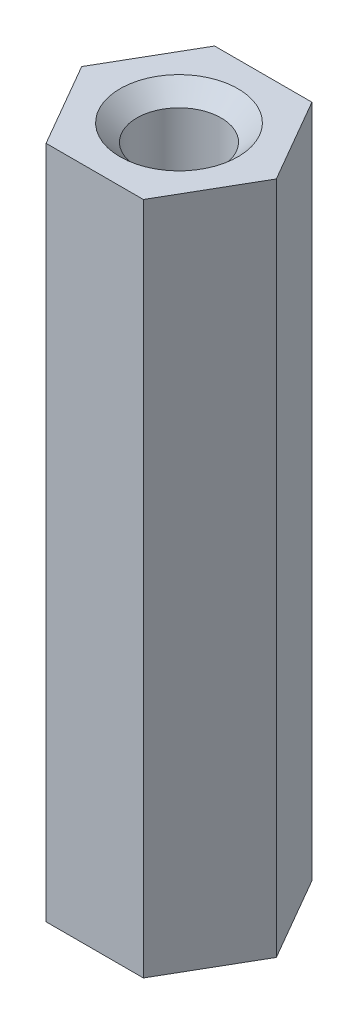
SolidWorks part; units mm, degrees
material "1,0503 (C45)"
ref_plane "Спереди" through (0, 0, 0) normal (0, 0, 1) x (1, 0, 0)
ref_plane "Сверху" through (0, 0, 0) normal (0, 1, 0) x (1, 0, 0)
ref_plane "Справа" through (0, 0, 0) normal (1, 0, 0) x (0, 0, -1)
sketch "Эскиз1" plane through (0, 0, 0) normal (0, 1, 0) x (1, 0, 0)
  line L1 (2.8868, 0) -> (1.4434, 2.5)
  line L2 (1.4434, 2.5) -> (-1.4434, 2.5)
  line L3 (-1.4434, 2.5) -> (-2.8868, 0)
  line L4 (-2.8868, 0) -> (-1.4434, -2.5)
  line L5 (-1.4434, -2.5) -> (1.4434, -2.5)
  line L6 (1.4434, -2.5) -> (2.8868, 0)
  circle A0 centre (0, 0) radius 2.5 construction
  dimension "D1" = 5
extrude "Бобышка-Вытянуть1" add sketch "Эскиз1" along normal blind 20
hole_wizard "Отверстие обработанное метчиком M3x0.51" positions "Эскиз3" profile "Эскиз2" tap size "M3x0.5" standard "Ansi (метрические)" end condition through all
sketch "Эскиз3" plane through (0, 20, 0) normal (0, 1, 0) x (-1, 0, 0)
  point P0 (0, 0)
sketch "Эскиз2" plane through (0, 20, 0) normal (1, 0, 0) x (0, 0, 1)
  line L0 (0, 0) -> (0, 20)
  line L1 (0, 20) -> (1.75, 20)
  line L2 (1.25, 19.5) -> (1.25, 0.5)
  line L3 (1.25, 0.5) -> (1.75, 0)
  line L5 (1.75, 0) -> (0, 0)
  line L6 (-1.25, 0.5) -> (-1.75, 0) construction
  line L7 (1.75, 20) -> (1.25, 19.5)
  line L8 (-1.75, 20) -> (-1.25, 19.5) construction
  line L11 (0, -6.35) -> (0, 107.95) construction
  dimension "Диаметр проходного сверла" = 2.5
  dimension "Глубина проходного сверла" = 20
  dimension "Диаметр передней зенковки" = 3.5
  dimension "Угол передней зенковки" = 90
  dimension "Диаметр задней зенковки" = 3.5
  dimension "Угол задней зенковки" = 90
cosmetic thread "Отверстие резьбы1"
